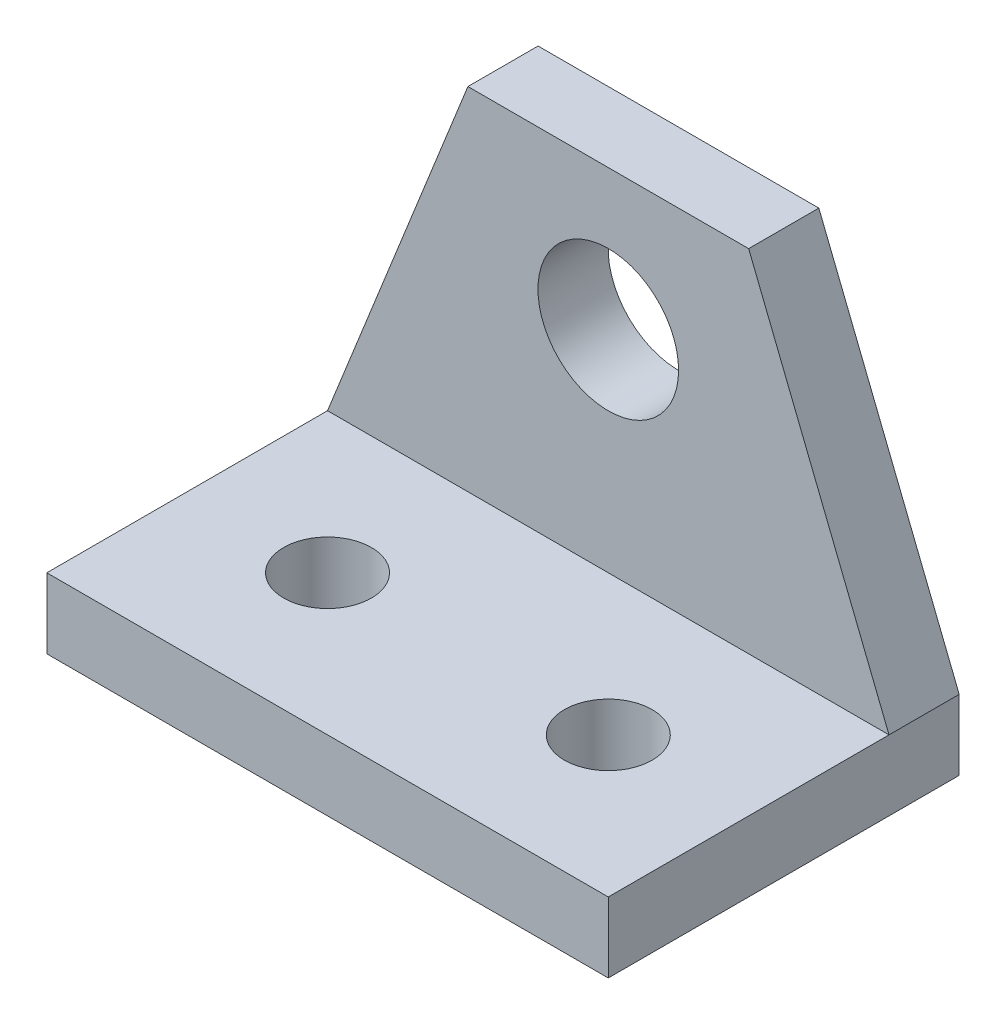
SolidWorks part; units mm, degrees
ref_plane "Front Plane" through (0, 0, 0) normal (0, 0, 1) x (1, 0, 0)
ref_plane "Top Plane" through (0, 0, 0) normal (0, 1, 0) x (1, 0, 0)
ref_plane "Right Plane" through (0, 0, 0) normal (1, 0, 0) x (0, 0, -1)
sketch "Sketch1" plane through (0, 0, 0) normal (1, 0, 0) x (0, 0, -1)
  line L1 (0, 0) -> (6.35, 0) construction
  line L2 (0, 0) -> (0, 38.1) construction
  line L3 (0, 38.1) -> (6.35, 38.1) construction
  line L4 (6.35, 0) -> (6.35, 38.1) construction
  line L5 (6.35, 0) -> (38.1, 0)
  line L6 (6.35, 0) -> (6.35, 6.35)
  line L7 (6.35, 6.35) -> (38.1, 6.35)
  line L8 (38.1, 0) -> (38.1, 6.35)
  line L9 (38.1, 6.35) -> (31.75, 6.35)
  line L10 (38.1, 6.35) -> (38.1, 38.1)
  line L11 (38.1, 38.1) -> (31.75, 38.1)
  line L12 (31.75, 6.35) -> (31.75, 38.1)
  dimension "D1" = 38.1
  dimension "D2" = 38.1
  dimension "D3" = 6.35
  dimension "D4" = 6.35
  dimension "D5" = 6.35
extrude "Boss-Extrude1" add sketch "Sketch1" along normal blind 50.8 contours L1 L4 L3 L2 | L5 L8 L7 L4 | L12 L7 L10 L11
sketch "Sketch2" plane through (0, 6.35, 0) normal (0, 1, 0) x (1, 0, 0)
  line L0 (0, 0) -> (0, 38.1) construction
  line L1 (0, 38.1) -> (50.8, 38.1) construction
  line L2 (50.8, 38.1) -> (50.8, 0) construction
  line L3 (50.8, 0) -> (0, 0) construction
  line L4 (0, 0) -> (0, 38.1) construction
  line L5 (50.8, 38.1) -> (0, 38.1) construction
  line L6 (50.8, 19.05) -> (0, 19.05) construction
  line L8 (50.8, 6.35) -> (50.8, 31.75) construction
  circle A0 centre (38.1, 19.05) radius 3.9687
  circle A1 centre (12.7, 19.05) radius 3.9688
  dimension "D2" = 7.9375
  dimension "D3" = 7.9375
  dimension "D1" = 19.05
  dimension "D4" = 12.7
  dimension "D5" = 25.4
extrude "Base Mounts" cut sketch "Sketch2" against normal up to next
sketch "Sketch3" plane through (0, 0, -31.75) normal (0, 0, 1) x (1, 0, 0)
  line L0 (0, 38.1) -> (0, 6.35) construction
  line L1 (0, 6.35) -> (50.8, 6.35) construction
  line L2 (50.8, 6.35) -> (50.8, 38.1) construction
  line L3 (50.8, 38.1) -> (0, 38.1) construction
  line L4 (0, 25.4) -> (50.8, 25.4) construction
  line L5 (0, 38.1) -> (0, 6.35) construction
  line L6 (50.8, 6.35) -> (50.8, 38.1) construction
  line L7 (50.8, 6.35) -> (50.8, 38.1)
  line L8 (50.8, 38.1) -> (38.1, 38.1)
  line L9 (38.1, 38.1) -> (50.8, 6.35)
  line L10 (0, 6.35) -> (0, 38.1)
  line L11 (0, 38.1) -> (12.7, 38.1)
  line L12 (12.7, 38.1) -> (0, 6.35)
  circle A0 centre (25.4, 25.4) radius 6.3627
  dimension "D1" = 12.7254
  dimension "D2" = 12.7
  dimension "D3" = 12.7
  dimension "D4" = 19.05
extrude "Pedal Hinge" cut sketch "Sketch3" against normal up to next
